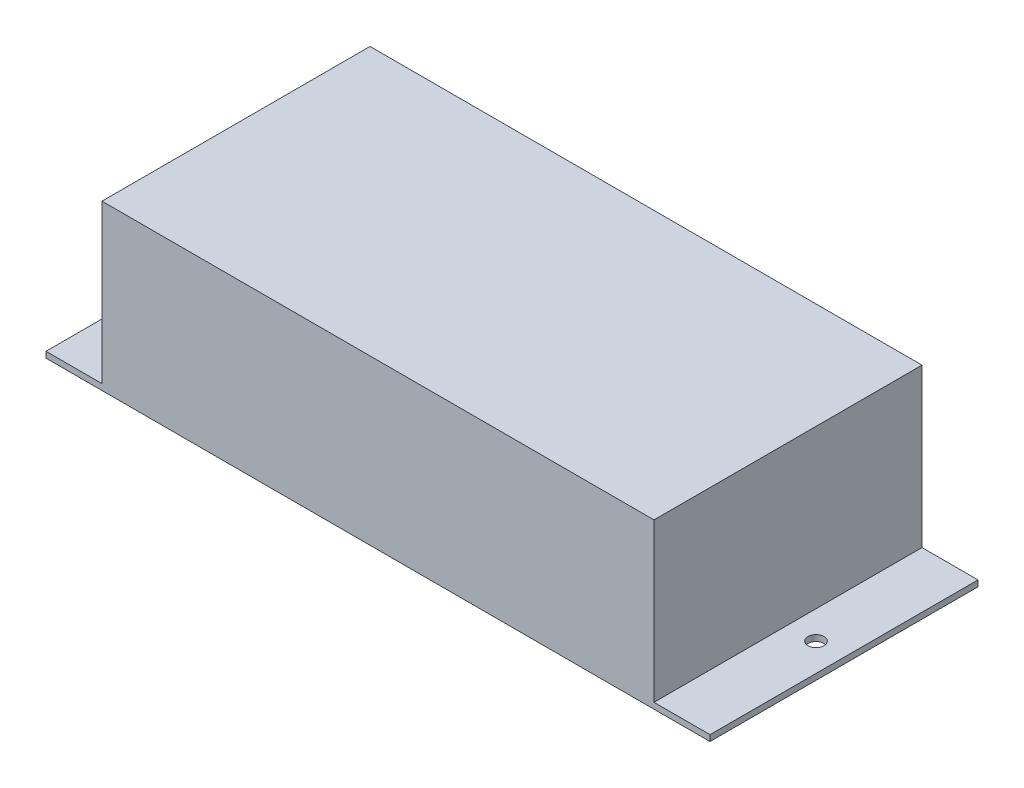
SolidWorks part; units mm, degrees
ref_plane "Ebene vorne" through (0, 0, 0) normal (0, 0, 1) x (1, 0, 0)
ref_plane "Ebene oben" through (0, 0, 0) normal (0, 1, 0) x (1, 0, 0)
ref_plane "Ebene rechts" through (0, 0, 0) normal (1, 0, 0) x (0, 0, -1)
sketch "Sketch2" plane through (0, 0, 0) normal (0, 0, 1) x (1, 0, 0)
  line L0 (83, 0) -> (-83, 0)
  line L1 (-83, 0) -> (-83, 1.5)
  line L2 (-83, 1.5) -> (-69, 1.5)
  line L3 (-69, 1.5) -> (-69, 41)
  line L4 (-69, 41) -> (69, 41)
  line L6 (0, 41) -> (0, 0) construction
  line L7 (69, 1.5) -> (69, 41)
  line L8 (83, 1.5) -> (69, 1.5)
  line L9 (83, 0) -> (83, 1.5)
  point P2 (-76, 1.5)
  point P10 (-69, 73.0722)
  point P11 (0, 0)
  point P12 (-69, 73.0722)
  point P13 (-69, 5.9562)
  dimension "D1" = 166
  dimension "D2" = 152
  dimension "D3" = 41
  dimension "D4" = 1.5
extrude "Boss-Extrude1" add sketch "Sketch2" along normal blind 67
hole_wizard "Ø4.0mm Dowel Hole1" positions "Sketch3" profile "Sketch4" hole size "Ø4.0" standard "DIN" end condition up to next
sketch "Sketch3" plane through (0, 1.5, 0) normal (0, 1, 0) x (1, 0, 0)
  line L0 (-76, 0) -> (-76, -67) construction
  line L1 (-69, 0) -> (-83, 0) construction
  line L2 (-69, -67) -> (-83, -67) construction
  line L4 (0, -22.55) -> (0, 22.55) construction
  point P0 (-76, -33.5)
  point P12 (0, 0)
  point P13 (0, 0)
  point P16 (76, -33.5)
sketch "Sketch4" plane through (-76, 1.5, 33.5) normal (1, 0, 0) x (0, 0, 1)
  line L0 (0, 0) -> (0, 1.5)
  line L1 (0, 1.5) -> (2, 1.5)
  line L2 (2, 1.5) -> (2, 0)
  line L5 (2, 0) -> (0, 0)
  line L11 (0, -6.35) -> (0, 107.95) construction
  dimension "Thru Hole Dia." = 4
  dimension "Thru Hole Depth" = 1.5
